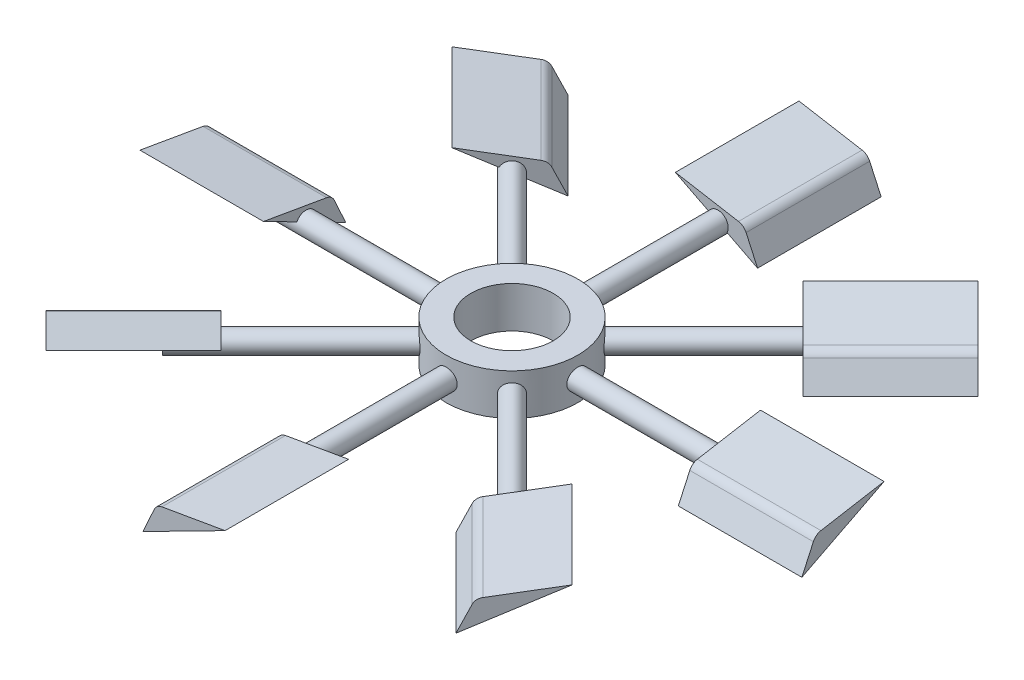
SolidWorks part; units mm, degrees
ref_plane "Alzado" through (0, 0, 0) normal (0, 0, 1) x (1, 0, 0)
ref_plane "Planta" through (0, 0, 0) normal (0, 1, 0) x (1, 0, 0)
ref_plane "Vista lateral" through (0, 0, 0) normal (1, 0, 0) x (0, 0, -1)
sketch "Sketch1" plane through (0, 0, 0) normal (0, 1, 0) x (1, 0, 0)
  circle A0 centre (0, 0) radius 12.7
  circle A1 centre (0, 0) radius 20.32
  dimension "D1" = 40.64
  dimension "D2" = 25.4
extrude "Boss-Extrude1" add sketch "Sketch1" along normal blind 12.7
sketch3d "3DSketch1" plane through (0, 0, 0) normal (0, 0, 1) x (1, 0, 0)
  dimension "D1" = 6.35
sketch "Sketch2" plane through (0, 6.35, 0) normal (0, 1, 0) x (1, 0, 0)
  line L0 (0, 0) -> (0, 81.4159) construction
  line L1 (0, 20.0704) -> (3.175, 20.0704)
  line L2 (0, 20.0704) -> (0, 76.2)
  line L3 (0, 76.2) -> (3.175, 76.2)
  line L4 (3.175, 20.0704) -> (3.175, 76.2)
  line L5 (0, 0) -> (42.7765, 0) construction
  circle A1 centre (0, 0) radius 20.32 construction
  point P4 (0, 0)
  point P11 (0, 81.4159)
  point P12 (42.7765, 0)
  dimension "D1" = 3.175
  dimension "D2" = 76.2
revolve "Revolve1" add sketch "Sketch2" angle 360 about L2
sketch3d "3DSketch3" plane through (0, 0, 0) normal (0, 0, 1) x (1, 0, 0)
  dimension "D1" = 12.7
sketch "Sketch3" plane through (0, 0, -76.2) normal (0, 0, -1) x (-1, 0, 0)
  line L0 (0, 6.35) -> (16.0671, 6.35) construction
  line L1 (0, 6.35) -> (11.1881, 12.0506) construction
  point P3 (0, 0)
  point P6 (0, 0)
  dimension "D1" = 27
sketch "Sketch4" plane through (0, 0, -63.5) normal (0, 0, -1) x (-1, 0, 0)
  line L1 (0, 6.35) -> (11.1881, 12.0506) construction
  line L3 (-12.221, 0.1231) -> (13.1263, 13.0382)
  line L4 (-7.4092, 9.7016) -> (-4.3533, 3.7043) construction
  line L5 (13.1263, 13.0382) -> (-6.3375, 9.6615)
  line L6 (-12.221, 0.1231) -> (-8.6817, 7.8548)
  arc A1 (-6.3375, 9.6615) -> (-8.6817, 7.8548) centre (-5.7948, 6.5332) ccw
  point P4 (0, 0)
  point P7 (0, 0)
  point P11 (0, 0)
  dimension "D3" = 6.35
  dimension "D5" = 2.794
  dimension "D1" = 28.448
  dimension "D2" = 13.716
  dimension "D4" = 8.636
extrude "Boss-Extrude2" add sketch "Sketch4" along normal blind 38.1
pattern_circular "CirPattern1" count 8 every 45 about axis through (0, 0, 0) along (0, 1, 0) of "Revolve1", "Boss-Extrude2"
